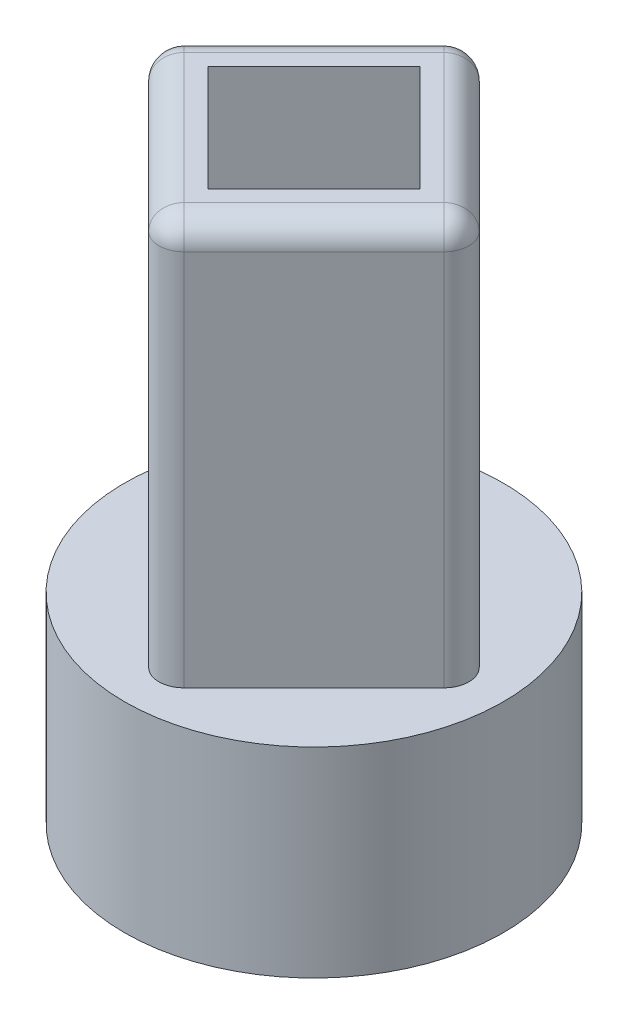
SolidWorks part; units mm, degrees
ref_plane "Front Plane" through (0, 0, 0) normal (0, 0, 1) x (1, 0, 0)
ref_plane "Top Plane" through (0, 0, 0) normal (0, 1, 0) x (1, 0, 0)
ref_plane "Right Plane" through (0, 0, 0) normal (1, 0, 0) x (0, 0, -1)
sketch "Sketch1" plane through (0, 0, 0) normal (0, 1, 0) x (1, 0, 0)
  circle A0 centre (0, 0) radius 7.575
  dimension "D1" = 15.15
extrude "Boss-Extrude1" add sketch "Sketch1" along normal blind 5.2
sketch "Sketch2" plane through (0, 0, 0) normal (0, -1, 0) x (1, 0, 0)
  line L0 (-4.3593, -1.3881) -> (0, -4.575)
  arc A0 (0, -4.575) -> (-4.3593, -1.3881) centre (0, 0) ccw
  dimension "D1" = 9.15
  dimension "D2" = 5.4
extrude "Cut-Extrude1" cut sketch "Sketch2" against normal blind 3.6
sketch "Sketch3" plane through (0, 3.6, 0) normal (0, -1, 0) x (1, 0, 0)
  line L0 (-1.9, 2.1577) -> (1.9, 2.1577)
  arc A0 (-1.9, 2.1577) -> (1.9, 2.1577) centre (0, 0) ccw
  dimension "D1" = 5.75
  dimension "D2" = 3.8
sketch "Sketch4" plane through (0, 5.2, 0) normal (0, 1, 0) x (1, 0, 0)
  line L1 (4.2426, 0) -> (0, 4.2426)
  line L2 (0, 4.2426) -> (-4.2426, 0)
  line L3 (-4.2426, 0) -> (0, -4.2426)
  line L4 (0, -4.2426) -> (4.2426, 0)
  line L5 (6.6114, 0) -> (0, 6.6114)
  line L6 (0, 6.6114) -> (-6.6114, 0)
  line L7 (-6.6114, 0) -> (0, -6.6114)
  line L8 (0, -6.6114) -> (6.6114, 0)
  circle A0 centre (0, 0) radius 3 construction
  circle A1 centre (0, 0) radius 4.675 construction
  dimension "D1" = 6
  dimension "D2" = 9.35
extrude "Boss-Extrude2" add sketch "Sketch4" along normal blind 18.9
fillet "Fillet1" radius 1 8 edges at (-3.3057, 24.1, -3.3057) (-3.3057, 24.1, 3.3057) (3.3057, 24.1, 3.3057) (3.3057, 24.1, -3.3057) (6.6114, 14.65, 0) (0, 14.65, 6.6114) (-6.6114, 14.65, 0) (0, 14.65, -6.6114)
sketch "Sketch5" plane through (0, 5.2, 0) normal (0, 1, 0) x (1, 0, 0)
  line L4 (0, -4.2426) -> (4.2426, 0)
  line L5 (4.2426, 0) -> (0, 4.2426)
  line L6 (0, 4.2426) -> (-4.2426, 0)
  line L7 (-4.2426, 0) -> (0, -4.2426)
  line L8 (0, -4.2426) -> (4.2426, 0)
  line L9 (4.2426, 0) -> (0, 4.2426)
  line L10 (0, 4.2426) -> (-4.2426, 0)
  line L11 (-4.2426, 0) -> (0, -4.2426)
  dimension "D1" = 0
extrude "Boss-Extrude3" add sketch "Sketch5" along normal blind 4.85
sketch "Sketch6" plane through (0, 10.05, 0) normal (0, 1, 0) x (1, 0, 0)
  circle A0 centre (0, 0) radius 1.875
  dimension "D1" = 3.75
extrude "Boss-Extrude4" add sketch "Sketch6" along normal blind 2.55
extrude "Cut-Extrude2" cut sketch "Sketch3" against normal blind 4
sketch "Sketch7" plane through (0, 5.2, 0) normal (0, 1, 0) x (1, 0, 0)
  line L0 (-5.9043, -0.7071) -> (-0.7071, -5.9043) construction
  line L1 (0.7071, -5.9043) -> (5.9043, -0.7071) construction
  line L2 (5.9043, 0.7071) -> (0.7071, 5.9043) construction
  line L3 (-0.7071, 5.9043) -> (-5.9043, 0.7071) construction
  line L4 (-5.9043, -0.7071) -> (-0.7071, -5.9043)
  line L5 (0.7071, -5.9043) -> (5.9043, -0.7071)
  line L6 (5.9043, 0.7071) -> (0.7071, 5.9043)
  line L7 (-0.7071, 5.9043) -> (-5.9043, 0.7071)
  arc A0 (-5.9043, 0.7071) -> (-5.9043, -0.7071) centre (-5.1972, 0) ccw construction
  circle A1 centre (0, 0) radius 7.575
  circle A2 centre (0, 0) radius 7.575
  arc A3 (-0.7071, -5.9043) -> (0.7071, -5.9043) centre (0, -5.1972) ccw construction
  arc A4 (5.9043, -0.7071) -> (5.9043, 0.7071) centre (5.1972, 0) ccw construction
  arc A5 (0.7071, 5.9043) -> (-0.7071, 5.9043) centre (0, 5.1972) ccw construction
  arc A6 (-5.9043, 0.7071) -> (-5.9043, -0.7071) centre (-5.1972, 0) ccw
  arc A7 (-0.7071, -5.9043) -> (0.7071, -5.9043) centre (0, -5.1972) ccw
  arc A8 (5.9043, -0.7071) -> (5.9043, 0.7071) centre (5.1972, 0) ccw
  arc A9 (0.7071, 5.9043) -> (-0.7071, 5.9043) centre (0, 5.1972) ccw
  dimension "D1" = 0
extrude "Boss-Extrude5" add sketch "Sketch7" along normal blind 2.8
